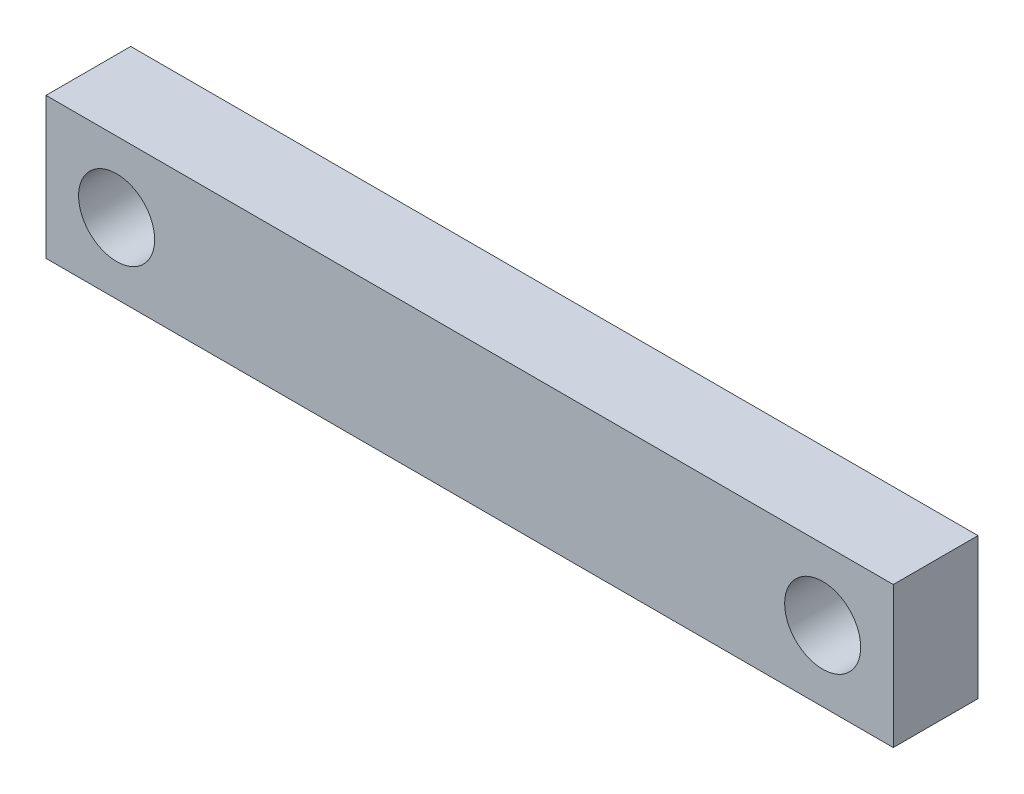
SolidWorks part; units mm, degrees
ref_plane "Plan de face" through (0, 0, 0) normal (0, 0, 1) x (1, 0, 0)
ref_plane "Plan de dessus" through (0, 0, 0) normal (0, 1, 0) x (1, 0, 0)
ref_plane "Plan de droite" through (0, 0, 0) normal (1, 0, 0) x (0, 0, -1)
sketch "Esquisse1" plane through (0, 0, 0) normal (0, 0, 1) x (1, 0, 0)
  line L0 (0, 2.5) -> (30, 2.5) construction
  line L1 (0, 0) -> (30, 0)
  line L2 (0, 0) -> (0, 5)
  line L3 (0, 5) -> (30, 5)
  line L4 (30, 0) -> (30, 5)
  line L5 (15, 0) -> (15, 5) construction
  circle A0 centre (2.5, 2.5) radius 1.3462
  circle A1 centre (27.5, 2.5) radius 1.3462
  dimension "D1" = 30
  dimension "D2" = 5
  dimension "D3" = 12.5
extrude "Boss.-Extru.1" add sketch "Esquisse1" along normal blind 3
